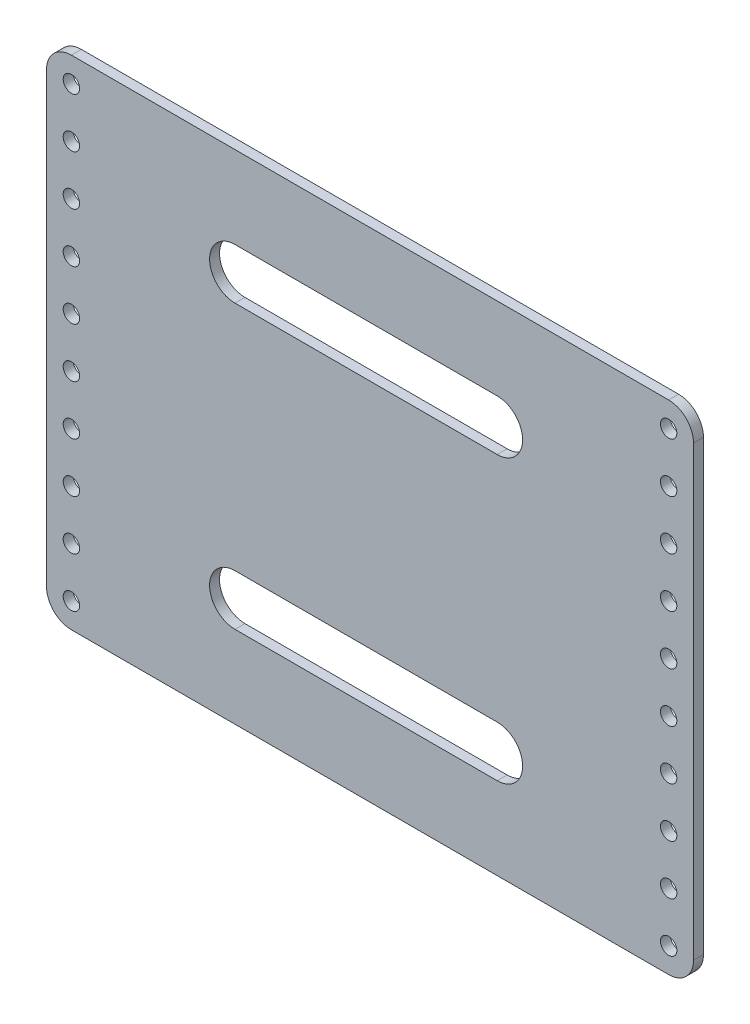
SolidWorks part; units mm, degrees
ref_plane "前视基准面" through (0, 0, 0) normal (0, 0, 1) x (1, 0, 0)
ref_plane "上视基准面" through (0, 0, 0) normal (0, 1, 0) x (1, 0, 0)
ref_plane "右视基准面" through (0, 0, 0) normal (1, 0, 0) x (0, 0, -1)
sketch "草图1" plane through (0, 0, 0) normal (0, 0, 1) x (1, 0, 0)
  line L1 (0, 0) -> (130, 0)
  line L2 (0, 0) -> (0, 100)
  line L3 (0, 100) -> (130, 100)
  line L4 (130, 0) -> (130, 100)
  dimension "D1" = 130
  dimension "D2" = 100
extrude "凸台-拉伸1" add sketch "草图1" along normal blind 2
fillet "圆角1" radius 5 4 edges at (0, 0, 1) (130, 0, 1) (130, 100, 1) (0, 100, 1)
sketch "草图2" plane through (0, 0, 2) normal (0, 0, 1) x (1, 0, 0)
  line L0 (0, 50) -> (130, 50) construction
  line L1 (5, 95) -> (5, 5) construction
  line L4 (0, 95) -> (0, 5)
  line L5 (5, 0) -> (125, 0)
  line L6 (130, 5) -> (130, 95)
  line L7 (125, 100) -> (5, 100)
  line L8 (0, 95) -> (0, 5)
  line L9 (5, 0) -> (125, 0)
  line L10 (130, 5) -> (130, 95)
  line L11 (125, 100) -> (5, 100)
  circle A0 centre (5, 95) radius 1.65
  arc A4 (0, 5) -> (5, 0) centre (5, 5) ccw
  arc A5 (125, 0) -> (130, 5) centre (125, 5) ccw
  arc A6 (130, 95) -> (125, 100) centre (125, 95) ccw
  arc A7 (5, 100) -> (0, 95) centre (5, 95) ccw
  arc A8 (0, 5) -> (5, 0) centre (5, 5) ccw
  arc A9 (125, 0) -> (130, 5) centre (125, 5) ccw
  arc A10 (130, 95) -> (125, 100) centre (125, 95) ccw
  arc A11 (5, 100) -> (0, 95) centre (5, 95) ccw
  point P13 (0, 0)
  dimension "D2" = 3.3
  dimension "D1" = 0
extrude "切除-拉伸1" cut sketch "草图2" against normal blind 2 contours A0
pattern_linear "阵列(线性)1" count 2 spacing 120 along (1, 0, 0) count 10 spacing 10 along (0, -1, 0) of "切除-拉伸1"
sketch "草图3" plane through (0, 0, 2) normal (0, 0, 1) x (1, 0, 0)
  line L0 (0, 50) -> (130, 50)
  line L1 (37.8662, 78.3802) -> (90.5571, 78.3802) construction
  line L2 (37.8662, 83.4813) -> (90.5571, 83.4813)
  line L3 (37.8662, 73.2792) -> (90.5571, 73.2792)
  line L4 (0, 95) -> (0, 5)
  line L5 (5, 0) -> (125, 0)
  line L6 (130, 5) -> (130, 95)
  line L7 (125, 100) -> (5, 100)
  line L8 (0, 95) -> (0, 5)
  line L9 (5, 0) -> (125, 0)
  line L10 (130, 5) -> (130, 95)
  line L11 (125, 100) -> (5, 100)
  line L12 (37.8662, 21.6198) -> (90.5571, 21.6198) construction
  line L13 (37.8662, 16.5187) -> (90.5571, 16.5187)
  line L14 (37.8662, 26.7208) -> (90.5571, 26.7208)
  arc A0 (37.8662, 83.4813) -> (37.8662, 73.2792) centre (37.8662, 78.3802) ccw
  arc A1 (90.5571, 73.2792) -> (90.5571, 83.4813) centre (90.5571, 78.3802) ccw
  arc A2 (37.8662, 16.5187) -> (37.8662, 26.7208) centre (37.8662, 21.6198) cw
  arc A3 (90.5571, 26.7208) -> (90.5571, 16.5187) centre (90.5571, 21.6198) cw
  arc A4 (0, 5) -> (5, 0) centre (5, 5) ccw
  arc A5 (125, 0) -> (130, 5) centre (125, 5) ccw
  arc A6 (130, 95) -> (125, 100) centre (125, 95) ccw
  arc A7 (5, 100) -> (0, 95) centre (5, 95) ccw
  arc A8 (0, 5) -> (5, 0) centre (5, 5) ccw
  arc A9 (125, 0) -> (130, 5) centre (125, 5) ccw
  arc A10 (130, 95) -> (125, 100) centre (125, 95) ccw
  arc A11 (5, 100) -> (0, 95) centre (5, 95) ccw
  point P15 (64.2116, 78.3802)
  point P23 (64.2116, 21.6198)
  dimension "D1" = 0
extrude "切除-拉伸2" cut sketch "草图3" against normal blind 2 contours L3 A1 L2 A0 | A3 L14 A2 L13
